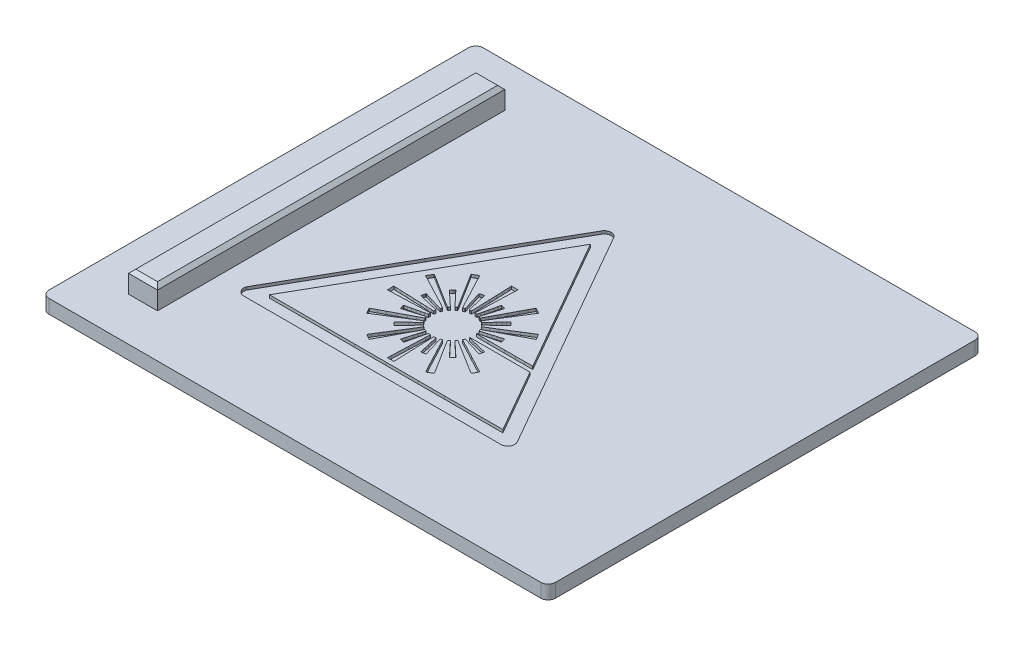
SolidWorks part; units mm, degrees
ref_plane "Front Plane" through (0, 0, 0) normal (0, 0, 1) x (1, 0, 0)
ref_plane "Top Plane" through (0, 0, 0) normal (0, 1, 0) x (1, 0, 0)
ref_plane "Right Plane" through (0, 0, 0) normal (1, 0, 0) x (0, 0, -1)
sketch "Sketch1" plane through (0, 0, 0) normal (0, 1, 0) x (1, 0, 0)
  line L1 (17.5, -15) -> (-17.5, -15)
  line L2 (17.5, -15) -> (17.5, 15)
  line L3 (17.5, 15) -> (-17.5, 15)
  line L4 (-17.5, -15) -> (-17.5, 15)
  line L5 (17.5, -15) -> (-17.5, 15) construction
  line L6 (17.5, 15) -> (-17.5, -15) construction
  point P0 (0, 0)
  dimension "D1" = 30
  dimension "D2" = 35
extrude "Boss-Extrude1" add sketch "Sketch1" along normal blind 0.95
fillet "Fillet1" radius 0.5 4 edges at (-17.5, 0.475, -15) (17.5, 0.475, -15) (17.5, 0.475, 15) (-17.5, 0.475, 15)
sketch "Sketch2" plane through (0, 0.95, 0) normal (0, 1, 0) x (1, 0, 0)
  line L7 (0, 0) -> (-13.5, 0) construction
  line L8 (-17.5, 14.5) -> (-17.5, -14.5) construction
  line L9 (-12.5, -12) -> (-14.5, -12)
  line L10 (-12.5, -12) -> (-12.5, 12)
  line L11 (-12.5, 12) -> (-14.5, 12)
  line L12 (-14.5, -12) -> (-14.5, 12)
  line L13 (-12.5, -12) -> (-14.5, 12) construction
  line L14 (-12.5, 12) -> (-14.5, -12) construction
  dimension "D1" = 24
  dimension "D2" = 2
  dimension "D3" = 3
extrude "Boss-Extrude2" add sketch "Sketch2" along normal blind 1.5
chamfer "Chamfer1" distance 0.25 angle 45 4 edges at (-13.5, 2.45, -12) (-12.5, 2.45, 0) (-13.5, 2.45, 12) (-14.5, 2.45, 0)
sketch "Sketch4" plane through (0, 0.95, 0) normal (0, 1, 0) x (1, 0, 0)
  line L0 (-9.5434, -5.1612) -> (-10.8497, -7.4519)
  line L1 (-10.4181, -8.1284) -> (-1.5285, -8.1285)
  line L2 (-1.5285, -8.1285) -> (7.3611, -8.1283)
  line L3 (7.7484, -7.3631) -> (3.3227, 0.3783)
  line L4 (3.3227, 0.3783) -> (-1.1105, 8.1325)
  line L5 (2.9967, -0.9727) -> (3.7735, -2.3341)
  line L6 (3.7721, -2.342) -> (3.2037, -2.344)
  line L7 (-0.1035, -2.307) -> (0.095, -2.2604)
  line L8 (1.0612, -2.0343) -> (1.2597, -1.987)
  line L9 (1.1727, -1.6869) -> (0.9773, -1.7453)
  line L10 (0.0274, -2.0322) -> (-0.1682, -2.0909)
  line L11 (-0.2094, -2.0255) -> (-0.2364, -1.9593)
  line L12 (-0.2364, -1.9593) -> (-0.1961, -1.9387)
  line L13 (-0.0829, -1.88) -> (1.0756, -1.267)
  line L14 (1.0756, -1.267) -> (2.2841, -0.6276)
  line L15 (2.055, -0.2524) -> (1.7026, -0.4714)
  line L16 (-0.0011, -1.5347) -> (-0.3524, -1.7512)
  line L17 (-0.3638, -1.7445) -> (-0.3758, -1.7294)
  line L18 (-0.3758, -1.7294) -> (-0.3902, -1.7114)
  line L19 (-0.3902, -1.7114) -> (-0.4058, -1.6918)
  line L20 (-0.4058, -1.6918) -> (-0.4452, -1.6421)
  line L21 (-0.4452, -1.6421) -> (-0.4032, -1.6054)
  line L22 (0.1217, -1.1166) -> (0.6047, -0.6646)
  line L23 (0.6047, -0.6646) -> (0.4958, -0.5553)
  line L24 (0.3758, -0.448) -> (0.2332, -0.5983)
  line L25 (-0.4548, -1.3302) -> (-0.5973, -1.4811)
  line L26 (-0.7053, -1.383) -> (-0.4843, -1.0296)
  line L27 (0.0507, -0.1763) -> (0.8072, 1.0284)
  line L28 (0.8072, 1.0284) -> (0.7698, 1.0506)
  line L29 (0.4158, 1.236) -> (0.2209, 0.8689)
  line L30 (-0.2494, -0.0193) -> (-0.5037, -0.5006)
  line L31 (-0.5037, -0.5006) -> (-0.7181, -0.9062)
  line L32 (-0.7181, -0.9062) -> (-0.9128, -1.2745)
  line L33 (-1.0495, -1.2211) -> (-0.9911, -1.0254)
  line L34 (-0.7038, -0.0755) -> (-0.6451, 0.1197)
  line L35 (-0.9443, 0.2198) -> (-0.9918, 0.0178)
  line L36 (-1.2195, -0.9597) -> (-1.2669, -1.162)
  line L37 (-1.3411, -1.1559) -> (-1.4119, -1.1454)
  line L38 (-1.4119, -1.1454) -> (-1.3648, 0.1365)
  line L39 (-1.3648, 0.1365) -> (-1.3463, 0.6384)
  line L40 (-1.3463, 0.6384) -> (-1.3296, 1.0858)
  line L41 (-1.3296, 1.0858) -> (-1.3154, 1.4634)
  line L42 (-1.3112, 1.5682) -> (-1.3047, 1.718)
  line L43 (-1.3047, 1.718) -> (-1.5287, 1.718)
  line L44 (-1.5287, 1.718) -> (-1.7526, 1.718)
  line L45 (-1.7526, 1.718) -> (-1.7461, 1.5682)
  line L46 (-1.7419, 1.4634) -> (-1.7277, 1.0858)
  line L47 (-1.7277, 1.0858) -> (-1.711, 0.6384)
  line L48 (-1.711, 0.6384) -> (-1.6925, 0.1365)
  line L49 (-1.6925, 0.1365) -> (-1.6454, -1.1454)
  line L50 (-1.6454, -1.1454) -> (-1.7162, -1.1559)
  line L51 (-1.7904, -1.162) -> (-1.8378, -0.9597)
  line L52 (-2.0655, 0.0178) -> (-2.1129, 0.2198)
  line L53 (-2.4122, 0.1196) -> (-2.3535, -0.0755)
  line L54 (-2.0662, -1.0254) -> (-2.0078, -1.2211)
  line L55 (-2.1445, -1.2745) -> (-2.3392, -0.9062)
  line L56 (-2.3392, -0.9062) -> (-2.5536, -0.5006)
  line L57 (-2.5536, -0.5006) -> (-2.808, -0.0193)
  line L58 (-3.2782, 0.8688) -> (-3.4731, 1.236)
  line L59 (-3.8523, 1.0121) -> (-3.1728, -0.0735)
  line L60 (-2.4601, -1.4812) -> (-2.6026, -1.3302)
  line L61 (-3.2905, -0.5983) -> (-3.4331, -0.448)
  line L62 (-3.5529, -0.5553) -> (-3.6617, -0.6645)
  line L63 (-3.6617, -0.6645) -> (-3.1893, -1.1064)
  line L64 (-2.6644, -1.5952) -> (-2.612, -1.642)
  line L65 (-2.612, -1.642) -> (-2.6515, -1.6917)
  line L66 (-2.6515, -1.6917) -> (-2.6671, -1.7114)
  line L67 (-2.6671, -1.7114) -> (-2.6814, -1.7293)
  line L68 (-2.6814, -1.7293) -> (-2.6934, -1.7444)
  line L69 (-2.7045, -1.751) -> (-3.0556, -1.5344)
  line L70 (-4.7586, -0.4715) -> (-5.1107, -0.2528)
  line L71 (-5.3431, -0.626) -> (-4.1477, -1.2585)
  line L72 (-4.1477, -1.2585) -> (-3.0399, -1.8445)
  line L73 (-4.082, -1.73) -> (-4.2269, -1.6871)
  line L74 (-4.3178, -1.9871) -> (-4.1175, -2.0344)
  line L75 (-3.1457, -2.2616) -> (-2.9453, -2.3088)
  line L76 (-2.9449, -2.386) -> (-2.9548, -2.4579)
  line L77 (-2.9548, -2.4579) -> (-3.0469, -2.4523)
  line L78 (-3.1153, -2.4489) -> (-3.4805, -2.4352)
  line L79 (-4.3938, -2.4018) -> (-4.8807, -2.3843)
  line L80 (-4.8807, -2.3843) -> (-5.3046, -2.3689)
  line L81 (-5.3046, -2.3689) -> (-5.6696, -2.3557)
  line L82 (-5.7324, -2.3532) -> (-5.8162, -2.3496)
  line L83 (-5.8162, -2.3496) -> (-5.8162, -2.5713)
  line L84 (-5.8162, -2.5713) -> (-5.8162, -2.793)
  line L85 (-5.8162, -2.793) -> (-5.7882, -2.793)
  line L86 (-5.7659, -2.7926) -> (-5.3686, -2.778)
  line L87 (-5.3686, -2.778) -> (-4.9228, -2.7617)
  line L88 (-4.9228, -2.7617) -> (-4.3989, -2.7422)
  line L89 (-4.3989, -2.7422) -> (-3.8739, -2.7228)
  line L90 (-3.4251, -2.7064) -> (-3.0286, -2.692)
  line L91 (-2.9957, -2.6914) -> (-2.9539, -2.6914)
  line L92 (-2.9539, -2.6914) -> (-2.9443, -2.7625)
  line L93 (-2.9632, -2.8411) -> (-3.1571, -2.8861)
  line L94 (-3.1571, -2.8861) -> (-3.3755, -2.9367)
  line L95 (-3.3755, -2.9367) -> (-3.6318, -2.9959)
  line L96 (-4.1065, -3.1064) -> (-4.3002, -3.1521)
  line L97 (-4.2607, -3.4161) -> (-4.2485, -3.4587)
  line L98 (-4.2442, -3.4621) -> (-4.0468, -3.4033)
  line L99 (-3.0907, -3.1146) -> (-2.8934, -3.0551)
  line L100 (-2.8422, -3.1957) -> (-3.2065, -3.3883)
  line L101 (-3.2065, -3.3883) -> (-3.6109, -3.602)
  line L102 (-3.6109, -3.602) -> (-4.089, -3.8546)
  line L103 (-4.9705, -4.3213) -> (-5.3344, -4.5147)
  line L104 (-3.614, -3.9567) -> (-2.716, -3.3947)
  line L105 (-3.1397, -3.9922) -> (-3.664, -4.4828)
  line L106 (-3.664, -4.4828) -> (-3.5512, -4.5955)
  line L107 (-3.5512, -4.5955) -> (-3.4383, -4.7082)
  line L108 (-3.4383, -4.7082) -> (-3.3903, -4.6548)
  line L109 (-3.3561, -4.6176) -> (-3.2266, -4.4787)
  line L110 (-2.9005, -4.13) -> (-2.4587, -3.6585)
  line L111 (-2.4587, -3.6585) -> (-2.4331, -3.6771)
  line L112 (-2.3754, -3.7244) -> (-2.3433, -3.7531)
  line L113 (-2.3433, -3.7531) -> (-3.1034, -4.9619)
  line L114 (-3.4773, -6.3863) -> (-3.2825, -6.0217)
  line L115 (-2.8139, -5.1386) -> (-2.5602, -4.6585)
  line L116 (-2.5602, -4.6585) -> (-2.3455, -4.2525)
  line L117 (-2.3455, -4.2525) -> (-2.152, -3.8866)
  line L118 (-2.0107, -3.9264) -> (-2.0692, -4.1251)
  line L119 (-2.1098, -5.3505) -> (-2.0633, -5.1521)
  line L120 (-1.8378, -4.1869) -> (-1.7907, -3.9884)
  line L121 (-1.7153, -3.9881) -> (-1.6471, -3.997)
  line L122 (-1.6471, -3.997) -> (-1.6491, -4.0732)
  line L123 (-1.6571, -4.3229) -> (-1.6981, -5.4408)
  line L124 (-1.6981, -5.4408) -> (-1.7408, -6.5997)
  line L125 (-1.7474, -6.7427) -> (-1.7536, -6.857)
  line L126 (-1.7536, -6.857) -> (-1.5287, -6.857)
  line L127 (-1.5287, -6.857) -> (-1.3037, -6.857)
  line L128 (-1.3037, -6.857) -> (-1.3099, -6.7427)
  line L129 (-1.3165, -6.5997) -> (-1.3592, -5.4408)
  line L130 (-1.3592, -5.4408) -> (-1.4002, -4.3229)
  line L131 (-1.4082, -4.0732) -> (-1.4102, -3.997)
  line L132 (-1.4102, -3.997) -> (-1.342, -3.9881)
  line L133 (-1.2666, -3.9884) -> (-1.2195, -4.1869)
  line L134 (-0.994, -5.1521) -> (-0.9475, -5.3505)
  line L135 (-0.6854, -5.3041) -> (-0.6423, -5.2921)
  line L136 (-0.6388, -5.2874) -> (-0.6982, -5.0883)
  line L137 (-0.9875, -4.1243) -> (-1.0451, -3.9262)
  line L138 (-0.9171, -3.873) -> (-0.7208, -4.2399)
  line L139 (0.2239, -6.019) -> (0.4202, -6.3862)
  line L140 (0.7837, -6.1347) -> (0.5825, -5.8145)
  line L141 (0.5825, -5.8145) -> (0.357, -5.4555)
  line L142 (0.357, -5.4555) -> (0.0919, -5.0333)
  line L143 (0.0919, -5.0333) -> (-0.1764, -4.606)
  line L144 (-0.1764, -4.606) -> (-0.412, -4.2308)
  line L145 (-0.412, -4.2308) -> (-0.613, -3.9106)
  line L146 (-0.613, -3.9106) -> (-0.656, -3.8423)
  line L147 (-0.656, -3.8423) -> (-0.7149, -3.7485)
  line L148 (-0.7149, -3.7485) -> (-0.6566, -3.7036)
  line L149 (-0.6566, -3.7036) -> (-0.5983, -3.6588)
  line L150 (-0.5983, -3.6588) -> (-0.1567, -4.1302)
  line L151 (0.1693, -4.4787) -> (0.2988, -4.6176)
  line L152 (0.333, -4.6548) -> (0.381, -4.7082)
  line L153 (0.381, -4.7082) -> (0.494, -4.5953)
  line L154 (0.494, -4.5953) -> (0.607, -4.4825)
  line L155 (0.607, -4.4825) -> (0.0827, -3.9919)
  line L156 (-0.3426, -3.3942) -> (0.0065, -3.6118)
  line L157 (0.8491, -4.1392) -> (1.3065, -4.4262)
  line L158 (1.6946, -4.6694) -> (2.0425, -4.8873)
  line L159 (2.2741, -4.5122) -> (1.1103, -3.8955)
  line L160 (-0.1995, -3.2034) -> (-0.2368, -3.1842)
  line L161 (-0.2368, -3.1842) -> (-0.2085, -3.1181)
  line L162 (-0.151, -3.0581) -> (0.0437, -3.1167)
  line L163 (0.992, -3.4034) -> (1.1873, -3.4618)
  line L164 (1.1913, -3.4587) -> (1.2034, -3.416)
  line L165 (1.2428, -3.1518) -> (1.0507, -3.1062)
  line L166 (0.5795, -2.9959) -> (0.3248, -2.9369)
  line L167 (0.3248, -2.9369) -> (0.1068, -2.8862)
  line L168 (0.1068, -2.8862) -> (-0.0854, -2.8416)
  line L169 (1.9618, -2.793) -> (4.0376, -2.793)
  line L170 (4.0376, -2.793) -> (5.2873, -4.9799)
  line L171 (5.2873, -4.9799) -> (6.537, -7.1669)
  line L172 (6.537, -7.1669) -> (2.5041, -7.1694)
  line L173 (-5.5617, -7.1694) -> (-9.5948, -7.1669)
  line L174 (-9.5948, -7.1669) -> (-5.5643, -0.1137)
  line L175 (-2.7162, 4.8677) -> (-1.5318, 6.9377)
  line L176 (-1.5255, 6.9376) -> (-0.7469, 5.5776)
  arc A0 (-1.6369, 8.3692) -> (-1.6998, 8.3486) centre (-1.5136, 7.886) ccw
  arc A1 (-1.6998, 8.3486) -> (-1.7595, 8.3199) centre (-1.5135, 7.8856) ccw
  arc A2 (-1.7595, 8.3199) -> (-1.8144, 8.2837) centre (-1.518, 7.8935) ccw
  arc A3 (-1.8144, 8.2837) -> (-1.8629, 8.2412) centre (-1.5384, 7.9204) ccw
  arc A4 (-1.8629, 8.2412) -> (-1.9252, 8.1593) centre (-1.5779, 7.9595) ccw
  arc A5 (-1.9252, 8.1593) -> (-2.6587, 6.8837) centre (2003.3878, -1145.6798) ccw
  arc A6 (-2.6587, 6.8837) -> (-3.797, 4.8977) centre (957.1377, -544.5622) ccw
  arc A7 (-3.797, 4.8977) -> (-6.3845, 0.3712) centre (19505.5643, -11150.5144) ccw
  arc A8 (-6.3845, 0.3712) -> (-8.0978, -2.628) centre (8611.002, -4924.3902) ccw
  arc A9 (-8.0978, -2.628) -> (-9.5434, -5.1612) centre (4419.9804, -2531.1887) ccw
  arc A10 (-10.8497, -7.4519) -> (-10.8687, -7.492) centre (-10.5976, -7.5957) ccw
  arc A11 (-10.8687, -7.492) -> (-10.8844, -7.5491) centre (-10.5798, -7.6025) ccw
  arc A12 (-10.8844, -7.5491) -> (-10.8931, -7.6209) centre (-10.2161, -7.6662) ccw
  arc A13 (-10.8931, -7.6209) -> (-10.8941, -7.6933) centre (-10.2153, -7.6662) ccw
  arc A14 (-10.8941, -7.6933) -> (-10.8861, -7.7522) centre (-10.581, -7.6808) ccw
  arc A15 (-10.8861, -7.7522) -> (-10.8392, -7.8745) centre (-10.4163, -7.6423) ccw
  arc A16 (-10.8392, -7.8745) -> (-10.7608, -7.9807) centre (-10.4046, -7.6358) ccw
  arc A17 (-10.7608, -7.9807) -> (-10.6573, -8.0623) centre (-10.4054, -7.6365) ccw
  arc A18 (-10.6573, -8.0623) -> (-10.5368, -8.1129) centre (-10.4138, -7.6507) ccw
  arc A19 (-10.5368, -8.1129) -> (-10.4181, -8.1284) centre (-10.4181, -7.6668) ccw
  arc A20 (7.3611, -8.1283) -> (7.4798, -8.1128) centre (7.3611, -7.6667) ccw
  arc A21 (7.4798, -8.1128) -> (7.5416, -8.0924) centre (7.3394, -7.5853) ccw
  arc A22 (7.5416, -8.0924) -> (7.5952, -8.0661) centre (7.3973, -7.7305) ccw
  arc A23 (7.5952, -8.0661) -> (7.6454, -8.0312) centre (7.3865, -7.7123) ccw
  arc A24 (7.6454, -8.0312) -> (7.6968, -7.9848) centre (7.2209, -7.5081) ccw
  arc A25 (7.6968, -7.9848) -> (7.7643, -7.9036) centre (7.2966, -7.584) ccw
  arc A26 (7.7643, -7.9036) -> (7.8096, -7.8169) centre (7.4202, -7.6685) ccw
  arc A27 (7.8096, -7.8169) -> (7.8332, -7.7228) centre (7.4266, -7.6709) ccw
  arc A28 (7.8332, -7.7228) -> (7.8362, -7.6192) centre (7.3064, -7.6556) ccw
  arc A29 (7.8362, -7.6192) -> (7.8323, -7.5825) centre (7.3381, -7.6534) ccw
  arc A30 (7.8323, -7.5825) -> (7.8257, -7.5458) centre (7.3205, -7.6559) ccw
  arc A31 (7.8257, -7.5458) -> (7.8168, -7.5113) centre (7.3592, -7.6475) ccw
  arc A32 (7.8168, -7.5113) -> (7.8061, -7.481) centre (7.5136, -7.6015) ccw
  arc A33 (7.8061, -7.481) -> (7.7484, -7.3631) centre (6.8601, -7.8709) ccw
  arc A34 (-1.1105, 8.1325) -> (-1.1678, 8.2158) centre (-1.6361, 7.832) ccw
  arc A35 (-1.1678, 8.2158) -> (-1.2072, 8.2563) centre (-1.4239, 8.0059) ccw
  arc A36 (-1.2072, 8.2563) -> (-1.2581, 8.2953) centre (-1.5624, 7.8458) ccw
  arc A37 (-1.2581, 8.2953) -> (-1.3146, 8.329) centre (-1.5764, 7.8251) ccw
  arc A38 (-1.3146, 8.329) -> (-1.3712, 8.3535) centre (-1.5172, 7.9391) ccw
  arc A39 (-1.3712, 8.3535) -> (-1.433, 8.3696) centre (-1.4976, 7.9947) ccw
  arc A40 (-1.433, 8.3696) -> (-1.5059, 8.378) centre (-1.5449, 7.7202) ccw
  arc A41 (-1.5059, 8.378) -> (-1.578, 8.3782) centre (-1.5439, 7.7373) ccw
  arc A42 (-1.578, 8.3782) -> (-1.6369, 8.3692) centre (-1.5618, 8.0749) ccw
  arc A43 (2.1415, 0.5253) -> (1.1256, 2.3034) centre (-7662.7608, -4377.185) ccw
  arc A44 (2.9967, -0.9727) -> (2.1415, 0.5253) centre (-3858.2555, -2204.287) ccw
  arc A45 (3.7749, -2.3393) -> (3.7735, -2.3341) centre (3.7645, -2.3393) ccw
  arc A46 (3.7721, -2.342) -> (3.7749, -2.3393) centre (3.7721, -2.3393) ccw
  arc A47 (2.576, -2.3455) -> (3.2037, -2.344) centre (2.1994, 289.3373) ccw
  arc A48 (1.8303, -2.346) -> (2.576, -2.3455) centre (1.8308, 574.7754) ccw
  arc A49 (0.6912, -2.3455) -> (1.8303, -2.346) centre (1.831, 1496.5027) ccw
  arc A50 (0.2044, -2.3434) -> (0.6912, -2.3455) centre (0.7423, 64.8165) ccw
  arc A51 (-0.1055, -2.3406) -> (0.2044, -2.3434) centre (1.2953, 133.8322) ccw
  arc A52 (-0.1202, -2.3303) -> (-0.1055, -2.3406) centre (-0.1054, -2.3246) ccw
  arc A53 (-0.1216, -2.324) -> (-0.1202, -2.3303) centre (-0.1009, -2.3229) ccw
  arc A54 (-0.1208, -2.3179) -> (-0.1216, -2.324) centre (-0.1047, -2.3231) ccw
  arc A55 (-0.118, -2.3131) -> (-0.1208, -2.3179) centre (-0.1075, -2.3222) ccw
  arc A56 (-0.1137, -2.3101) -> (-0.118, -2.3131) centre (-0.11, -2.3201) ccw
  arc A57 (-0.1035, -2.307) -> (-0.1137, -2.3101) centre (-0.0837, -2.3911) ccw
  arc A58 (0.3174, -2.2083) -> (0.095, -2.2604) centre (35.753, -154.1712) ccw
  arc A59 (0.5792, -2.1474) -> (0.3174, -2.2083) centre (67.8233, -291.7028) ccw
  arc A60 (0.5792, -2.1474) -> (0.8404, -2.0865) centre (-28.2068, 121.8061) ccw
  arc A61 (0.8404, -2.0865) -> (1.0612, -2.0343) centre (-14.0928, 61.6071) ccw
  arc A62 (1.2597, -1.987) -> (1.2647, -1.9842) centre (1.2572, -1.9766) ccw
  arc A63 (1.2647, -1.9842) -> (1.2669, -1.9769) centre (1.2592, -1.9786) ccw
  arc A64 (1.2669, -1.9769) -> (1.2501, -1.9048) centre (-10.8857, -4.7599) ccw
  arc A65 (1.2501, -1.9048) -> (1.2293, -1.8204) centre (-2.5718, -2.8039) ccw
  arc A66 (1.2293, -1.8204) -> (1.2023, -1.7186) centre (-6.9068, -3.9257) ccw
  arc A67 (1.2023, -1.7186) -> (1.198, -1.7059) centre (1.0965, -1.7474) ccw
  arc A68 (1.198, -1.7059) -> (1.1925, -1.6953) centre (1.1318, -1.7329) ccw
  arc A69 (1.1925, -1.6953) -> (1.1868, -1.6878) centre (1.151, -1.721) ccw
  arc A70 (1.1868, -1.6878) -> (1.1818, -1.6856) centre (1.1818, -1.6924) ccw
  arc A71 (1.1818, -1.6856) -> (1.1727, -1.6869) centre (1.1818, -1.7173) ccw
  arc A72 (0.9773, -1.7453) -> (0.7589, -1.8109) centre (23.3046, -76.4545) ccw
  arc A73 (0.7589, -1.8109) -> (0.5018, -1.8888) centre (44.0077, -144.998) ccw
  arc A74 (0.245, -1.9667) -> (0.5018, -1.8888) centre (-58.8196, 193.2458) ccw
  arc A75 (0.0274, -2.0322) -> (0.245, -1.9667) centre (-30.1625, 98.532) ccw
  arc A76 (-0.1745, -2.0918) -> (-0.1682, -2.0909) centre (-0.1741, -2.0713) ccw
  arc A77 (-0.1786, -2.0894) -> (-0.1745, -2.0918) centre (-0.1744, -2.0869) ccw
  arc A78 (-0.188, -2.0723) -> (-0.1786, -2.0894) centre (0.2905, -1.8206) ccw
  arc A79 (-0.1985, -2.0508) -> (-0.188, -2.0723) centre (0.1679, -1.8851) ccw
  arc A80 (-0.2094, -2.0255) -> (-0.1985, -2.0508) centre (0.4605, -1.7527) ccw
  arc A81 (-0.1961, -1.9387) -> (-0.0829, -1.88) centre (-4.0968, 5.7073) ccw
  arc A82 (2.2841, -0.6276) -> (2.2902, -0.6232) centre (2.2709, -0.6026) ccw
  arc A83 (2.2902, -0.6232) -> (2.2921, -0.6102) centre (2.283, -0.6155) ccw
  arc A84 (2.2921, -0.6102) -> (2.1859, -0.4327) centre (-51.793, -32.8523) ccw
  arc A85 (2.1859, -0.4327) -> (2.0794, -0.2562) centre (-47.1809, -30.0822) ccw
  arc A86 (2.0794, -0.2562) -> (2.0655, -0.249) centre (2.0666, -0.2639) ccw
  arc A87 (2.0655, -0.249) -> (2.055, -0.2524) centre (2.0673, -0.2722) ccw
  arc A88 (1.7026, -0.4714) -> (1.3116, -0.7151) centre (88.4426, -140.0595) ccw
  arc A89 (1.3116, -0.7151) -> (0.8498, -1.0044) centre (170.8631, -271.8705) ccw
  arc A90 (0.3884, -1.2931) -> (0.8498, -1.0044) centre (-97.4207, 155.5606) ccw
  arc A91 (-0.0011, -1.5347) -> (0.3884, -1.2931) centre (-49.1087, 78.0842) ccw
  arc A92 (-0.3592, -1.7501) -> (-0.3524, -1.7512) centre (-0.3551, -1.7468) ccw
  arc A93 (-0.3638, -1.7445) -> (-0.3592, -1.7501) centre (0.0296, -1.4296) ccw
  arc A94 (-0.4032, -1.6054) -> (-0.373, -1.5781) centre (-1.2663, -0.6173) ccw
  arc A95 (-0.373, -1.5781) -> (-0.2317, -1.4467) centre (-183.8711, 195.7959) ccw
  arc A96 (-0.2317, -1.4467) -> (-0.0664, -1.2925) centre (-96.7439, 102.2148) ccw
  arc A97 (-0.0664, -1.2925) -> (0.1217, -1.1166) centre (-162.832, 172.9716) ccw
  arc A98 (0.4958, -0.5553) -> (0.4536, -0.5134) centre (-3.2412, -4.2807) ccw
  arc A99 (0.4536, -0.5134) -> (0.4169, -0.4781) centre (-1.5288, -2.5346) ccw
  arc A100 (0.4169, -0.4781) -> (0.3847, -0.4478) centre (-6.2622, -7.5376) ccw
  arc A101 (0.3847, -0.4478) -> (0.3803, -0.446) centre (0.3803, -0.4525) ccw
  arc A102 (0.3803, -0.446) -> (0.3758, -0.448) centre (0.3803, -0.4523) ccw
  arc A103 (0.2332, -0.5983) -> (0.0752, -0.7655) centre (40.1718, -38.4763) ccw
  arc A104 (0.0752, -0.7655) -> (-0.1111, -0.9642) centre (78.5725, -74.5919) ccw
  arc A105 (-0.2974, -1.1629) -> (-0.1111, -0.9642) centre (-118.7489, 110.05) ccw
  arc A106 (-0.4548, -1.3302) -> (-0.2974, -1.1629) centre (-60.6317, 55.4845) ccw
  arc A107 (-0.6003, -1.4824) -> (-0.5973, -1.4811) centre (-0.6003, -1.4782) ccw
  arc A108 (-0.6131, -1.4778) -> (-0.6003, -1.4824) centre (-0.6003, -1.4624) ccw
  arc A109 (-0.6593, -1.4388) -> (-0.6131, -1.4778) centre (1.4298, 0.9909) ccw
  arc A110 (-0.7057, -1.3983) -> (-0.6593, -1.4388) centre (2.2094, 1.8976) ccw
  arc A111 (-0.7083, -1.3896) -> (-0.7057, -1.3983) centre (-0.7001, -1.3919) ccw
  arc A112 (-0.7053, -1.383) -> (-0.7083, -1.3896) centre (-0.6829, -1.397) ccw
  arc A113 (-0.2395, -0.6388) -> (-0.4843, -1.0296) centre (366.9365, -230.8756) ccw
  arc A114 (0.0507, -0.1763) -> (-0.2395, -0.6388) centre (718.1204, -451.0857) ccw
  arc A115 (0.7698, 1.0506) -> (0.6359, 1.1291) centre (-5.7165, -9.8696) ccw
  arc A116 (0.6359, 1.1291) -> (0.5248, 1.1916) centre (-2.2769, -3.9142) ccw
  arc A117 (0.5248, 1.1916) -> (0.4293, 1.2437) centre (-9.5731, -17.2105) ccw
  arc A118 (0.4293, 1.2437) -> (0.4204, 1.2423) centre (0.4257, 1.2371) ccw
  arc A119 (0.4204, 1.2423) -> (0.4158, 1.236) centre (0.4401, 1.2232) ccw
  arc A120 (0.2209, 0.8689) -> (0.0053, 0.4623) centre (341.2184, -180.1579) ccw
  arc A121 (0.0053, 0.4623) -> (-0.2494, -0.0193) centre (668.7742, -353.548) ccw
  arc A122 (-0.914, -1.2766) -> (-0.9128, -1.2745) centre (-0.9399, -1.2601) ccw
  arc A123 (-0.9171, -1.2776) -> (-0.914, -1.2766) centre (-0.9162, -1.2752) ccw
  arc A124 (-0.9799, -1.2531) -> (-0.9171, -1.2776) centre (11.8484, 31.4432) ccw
  arc A125 (-1.0401, -1.2293) -> (-0.9799, -1.2531) centre (3.8181, 10.976) ccw
  arc A126 (-1.0488, -1.2237) -> (-1.0401, -1.2293) centre (-1.0299, -1.2035) ccw
  arc A127 (-1.0495, -1.2211) -> (-1.0488, -1.2237) centre (-1.0471, -1.2219) ccw
  arc A128 (-0.926, -0.809) -> (-0.9911, -1.0254) centre (69.8666, -22.2011) ccw
  arc A129 (-0.8482, -0.5524) -> (-0.926, -0.809) centre (138.5664, -42.9606) ccw
  arc A130 (-0.8482, -0.5524) -> (-0.7701, -0.2949) centre (-224.3348, 67.4293) ccw
  arc A131 (-0.7701, -0.2949) -> (-0.7038, -0.0755) centre (-118.9631, 35.509) ccw
  arc A132 (-0.6451, 0.1197) -> (-0.6422, 0.1322) centre (-0.7388, 0.1479) ccw
  arc A133 (-0.6422, 0.1322) -> (-0.647, 0.1419) centre (-0.6515, 0.1337) ccw
  arc A134 (-0.647, 0.1419) -> (-0.6713, 0.1531) centre (-0.7419, -0.0331) ccw
  arc A135 (-0.6713, 0.1531) -> (-0.7136, 0.1671) centre (-0.8581, -0.3394) ccw
  arc A136 (-0.7136, 0.1671) -> (-0.7895, 0.188) centre (-1.9652, -4.2182) ccw
  arc A137 (-0.7895, 0.188) -> (-0.8471, 0.203) centre (-2.0715, -4.6167) ccw
  arc A138 (-0.8471, 0.203) -> (-0.8962, 0.215) centre (-1.4821, -2.2965) ccw
  arc A139 (-0.8962, 0.215) -> (-0.9392, 0.2249) centre (-3.3119, -10.14) ccw
  arc A140 (-0.9392, 0.2249) -> (-0.9425, 0.2237) centre (-0.9399, 0.2218) ccw
  arc A141 (-0.9425, 0.2237) -> (-0.9443, 0.2198) centre (-0.9341, 0.2175) ccw
  arc A142 (-0.9918, 0.0178) -> (-1.0442, -0.2061) centre (117.8398, -27.9011) ccw
  arc A143 (-1.0442, -0.2061) -> (-1.1058, -0.4713) centre (231.5081, -54.381) ccw
  arc A144 (-1.1673, -0.7363) -> (-1.1058, -0.4713) centre (-305.0395, 69.967) ccw
  arc A145 (-1.2195, -0.9597) -> (-1.1673, -0.7363) centre (-155.9438, 35.2761) ccw
  arc A146 (-1.2681, -1.1642) -> (-1.2669, -1.162) centre (-1.2712, -1.161) ccw
  arc A147 (-1.2701, -1.1649) -> (-1.2681, -1.1642) centre (-1.2698, -1.1624) ccw
  arc A148 (-1.2904, -1.1627) -> (-1.2701, -1.1649) centre (-0.8671, 2.5572) ccw
  arc A149 (-1.3138, -1.1598) -> (-1.2904, -1.1627) centre (-1.1633, -0.0461) ccw
  arc A150 (-1.3411, -1.1559) -> (-1.3138, -1.1598) centre (-1.0311, 0.9326) ccw
  arc A151 (-1.3112, 1.5682) -> (-1.3154, 1.4634) centre (16.9481, 0.7749) ccw
  arc A152 (-1.7419, 1.4634) -> (-1.7461, 1.5682) centre (-20.0054, 0.7749) ccw
  arc A153 (-1.7435, -1.1598) -> (-1.7162, -1.1559) centre (-2.0262, 0.9326) ccw
  arc A154 (-1.7669, -1.1627) -> (-1.7435, -1.1598) centre (-1.894, -0.0461) ccw
  arc A155 (-1.7872, -1.1649) -> (-1.7669, -1.1627) centre (-2.1903, 2.5572) ccw
  arc A156 (-1.7893, -1.1642) -> (-1.7872, -1.1649) centre (-1.7875, -1.1624) ccw
  arc A157 (-1.7904, -1.162) -> (-1.7893, -1.1642) centre (-1.7861, -1.161) ccw
  arc A158 (-1.89, -0.7363) -> (-1.8378, -0.9597) centre (152.8865, 35.2761) ccw
  arc A159 (-1.9515, -0.4713) -> (-1.89, -0.7363) centre (301.9822, 69.967) ccw
  arc A160 (-1.9515, -0.4713) -> (-2.0131, -0.2061) centre (-246.5718, -57.1635) ccw
  arc A161 (-2.0131, -0.2061) -> (-2.0655, 0.0178) centre (-126.9811, -29.3109) ccw
  arc A162 (-2.1129, 0.2198) -> (-2.1147, 0.2236) centre (-2.1228, 0.2175) ccw
  arc A163 (-2.1147, 0.2236) -> (-2.1178, 0.2247) centre (-2.1172, 0.2217) ccw
  arc A164 (-2.1178, 0.2247) -> (-2.1609, 0.2147) centre (0.4527, -10.9424) ccw
  arc A165 (-2.1609, 0.2147) -> (-2.21, 0.2028) centre (-1.5509, -2.3893) ccw
  arc A166 (-2.21, 0.2028) -> (-2.2677, 0.1877) centre (-0.9372, -4.8026) ccw
  arc A167 (-2.2677, 0.1877) -> (-2.3432, 0.1669) centre (-1.109, -4.1584) ccw
  arc A168 (-2.3432, 0.1669) -> (-2.3857, 0.1528) centre (-2.1961, -0.3488) ccw
  arc A169 (-2.3857, 0.1528) -> (-2.4103, 0.1416) centre (-2.3117, -0.0429) ccw
  arc A170 (-2.4103, 0.1416) -> (-2.4151, 0.132) centre (-2.406, 0.1335) ccw
  arc A171 (-2.4151, 0.132) -> (-2.4122, 0.1196) centre (-2.3183, 0.1479) ccw
  arc A172 (-2.3535, -0.0755) -> (-2.2873, -0.2949) centre (118.226, 36.215) ccw
  arc A173 (-2.2873, -0.2949) -> (-2.2091, -0.5524) centre (226.0242, 68.873) ccw
  arc A174 (-2.1313, -0.809) -> (-2.2091, -0.5524) centre (-141.6237, -42.9606) ccw
  arc A175 (-2.0662, -1.0254) -> (-2.1313, -0.809) centre (-72.9239, -22.2011) ccw
  arc A176 (-2.0085, -1.2237) -> (-2.0078, -1.2211) centre (-2.0102, -1.2219) ccw
  arc A177 (-2.0172, -1.2293) -> (-2.0085, -1.2237) centre (-2.0274, -1.2035) ccw
  arc A178 (-2.0774, -1.2531) -> (-2.0172, -1.2293) centre (-6.8587, 10.9352) ccw
  arc A179 (-2.1402, -1.2776) -> (-2.0774, -1.2531) centre (-14.8496, 31.305) ccw
  arc A180 (-2.1433, -1.2766) -> (-2.1402, -1.2776) centre (-2.1411, -1.2752) ccw
  arc A181 (-2.1445, -1.2745) -> (-2.1433, -1.2766) centre (-2.119, -1.261) ccw
  arc A182 (-2.808, -0.0193) -> (-3.0627, 0.4623) centre (-653.739, -343.9795) ccw
  arc A183 (-3.0627, 0.4623) -> (-3.2782, 0.8688) centre (-336.419, -176.0031) ccw
  arc A184 (-3.4731, 1.236) -> (-3.4777, 1.2422) centre (-3.4962, 1.2237) ccw
  arc A185 (-3.4777, 1.2422) -> (-3.4922, 1.2441) centre (-3.4862, 1.2337) ccw
  arc A186 (-3.4922, 1.2441) -> (-3.6713, 1.1404) centre (23.5435, -45.6589) ccw
  arc A187 (-3.6713, 1.1404) -> (-3.8499, 1.036) centre (22.9106, -44.5705) ccw
  arc A188 (-3.8499, 1.036) -> (-3.8562, 1.0221) centre (-3.8433, 1.0246) ccw
  arc A189 (-3.8562, 1.0221) -> (-3.8523, 1.0121) centre (-3.8272, 1.0278) ccw
  arc A190 (-3.1728, -0.0735) -> (-2.5706, -1.0349) centre (1904.8191, 1194.2151) ccw
  arc A191 (-2.5706, -1.0349) -> (-2.3553, -1.3759) centre (44.6014, 28.5251) ccw
  arc A192 (-2.3505, -1.3888) -> (-2.3553, -1.3759) centre (-2.3825, -1.3932) ccw
  arc A193 (-2.3531, -1.3999) -> (-2.3505, -1.3888) centre (-2.3664, -1.391) ccw
  arc A194 (-2.3652, -1.4133) -> (-2.3531, -1.3999) centre (-2.4048, -1.3653) ccw
  arc A195 (-2.3978, -1.4394) -> (-2.3652, -1.4133) centre (-3.2075, -0.3929) ccw
  arc A196 (-2.4194, -1.4558) -> (-2.3978, -1.4394) centre (-3.681, 0.2191) ccw
  arc A197 (-2.4382, -1.4697) -> (-2.4194, -1.4558) centre (-3.1162, -0.5307) ccw
  arc A198 (-2.4546, -1.4815) -> (-2.4382, -1.4697) centre (-4.2253, 1.0052) ccw
  arc A199 (-2.4573, -1.4824) -> (-2.4546, -1.4815) centre (-2.4573, -1.4776) ccw
  arc A200 (-2.4601, -1.4812) -> (-2.4573, -1.4824) centre (-2.4573, -1.4786) ccw
  arc A201 (-2.76, -1.1629) -> (-2.6026, -1.3302) centre (63.0691, 60.6258) ccw
  arc A202 (-2.9462, -0.9642) -> (-2.76, -1.1629) centre (126.4969, 120.1608) ccw
  arc A203 (-2.9462, -0.9642) -> (-3.1326, -0.7655) centre (-81.6298, -74.5919) ccw
  arc A204 (-3.1326, -0.7655) -> (-3.2905, -0.5983) centre (-43.2291, -38.4763) ccw
  arc A205 (-3.4331, -0.448) -> (-3.4376, -0.446) centre (-3.4376, -0.4523) ccw
  arc A206 (-3.4376, -0.446) -> (-3.442, -0.4478) centre (-3.4376, -0.4525) ccw
  arc A207 (-3.442, -0.4478) -> (-3.4742, -0.4781) centre (3.1903, -7.5149) ccw
  arc A208 (-3.4742, -0.4781) -> (-3.5108, -0.5134) centre (-1.5323, -2.5285) ccw
  arc A209 (-3.5108, -0.5134) -> (-3.5529, -0.5553) centre (0.1773, -4.2697) ccw
  arc A210 (-3.1893, -1.1064) -> (-3.0045, -1.2792) centre (178.3371, 192.9231) ccw
  arc A211 (-3.0045, -1.2792) -> (-2.8402, -1.4323) centre (110.0228, 119.764) ccw
  arc A212 (-2.8402, -1.4323) -> (-2.7011, -1.5618) centre (173.0885, 187.4868) ccw
  arc A213 (-2.7011, -1.5618) -> (-2.6644, -1.5952) centre (-1.0529, 0.2108) ccw
  arc A214 (-2.6979, -1.7499) -> (-2.6934, -1.7444) centre (-3.1401, -1.3874) ccw
  arc A215 (-2.7045, -1.751) -> (-2.6979, -1.7499) centre (-2.7018, -1.7467) ccw
  arc A216 (-3.4449, -1.2929) -> (-3.0556, -1.5344) centre (47.3172, 80.0901) ccw
  arc A217 (-3.9059, -1.0044) -> (-3.4449, -1.2929) centre (96.9187, 159.6123) ccw
  arc A218 (-3.9059, -1.0044) -> (-4.3675, -0.7152) centre (-164.7912, -257.2997) ccw
  arc A219 (-4.3675, -0.7152) -> (-4.7586, -0.4715) centre (-86.889, -132.7017) ccw
  arc A220 (-5.1107, -0.2528) -> (-5.1218, -0.2492) centre (-5.1239, -0.2742) ccw
  arc A221 (-5.1218, -0.2492) -> (-5.1366, -0.2567) centre (-5.1232, -0.2649) ccw
  arc A222 (-5.1366, -0.2567) -> (-5.2433, -0.4326) centre (38.4351, -26.8004) ccw
  arc A223 (-5.2433, -0.4326) -> (-5.3496, -0.6095) centre (42.7186, -29.3863) ccw
  arc A224 (-5.3496, -0.6095) -> (-5.3475, -0.623) centre (-5.3404, -0.615) ccw
  arc A225 (-5.3475, -0.623) -> (-5.3431, -0.626) centre (-5.3324, -0.6058) ccw
  arc A226 (-3.0399, -1.8445) -> (-2.8375, -1.9509) centre (18.8497, 39.5397) ccw
  arc A227 (-2.8295, -1.9585) -> (-2.8375, -1.9509) centre (-2.847, -1.9691) ccw
  arc A228 (-2.8274, -1.9684) -> (-2.8295, -1.9585) centre (-2.8426, -1.9664) ccw
  arc A229 (-2.8317, -1.9853) -> (-2.8274, -1.9684) centre (-2.8993, -1.9588) ccw
  arc A230 (-2.8472, -2.0233) -> (-2.8317, -1.9853) centre (-4.3694, -1.3836) ccw
  arc A231 (-2.8576, -2.048) -> (-2.8472, -2.0233) centre (-7.8817, 0.0925) ccw
  arc A232 (-2.8668, -2.0693) -> (-2.8576, -2.048) centre (-5.7374, -0.821) ccw
  arc A233 (-2.8748, -2.0877) -> (-2.8668, -2.0693) centre (-9.5871, 0.853) ccw
  arc A234 (-2.8764, -2.0906) -> (-2.8748, -2.0877) centre (-2.8916, -2.0803) ccw
  arc A235 (-2.8819, -2.0926) -> (-2.8764, -2.0906) centre (-2.8805, -2.0879) ccw
  arc A236 (-3.0153, -2.0529) -> (-2.8819, -2.0926) centre (28.7721, 104.5154) ccw
  arc A237 (-3.2246, -1.9898) -> (-3.0153, -2.0529) centre (8.8022, 37.5658) ccw
  arc A238 (-3.7272, -1.8369) -> (-3.2246, -1.9898) centre (288.3979, 957.1437) ccw
  arc A239 (-3.7272, -1.8369) -> (-3.9186, -1.7789) centre (-24.1057, -68.7348) ccw
  arc A240 (-3.9186, -1.7789) -> (-4.082, -1.73) centre (-14.6402, -37.3397) ccw
  arc A241 (-4.2269, -1.6871) -> (-4.2375, -1.6856) centre (-4.2375, -1.7229) ccw
  arc A242 (-4.2375, -1.6856) -> (-4.2432, -1.6876) centre (-4.2375, -1.6947) ccw
  arc A243 (-4.2432, -1.6876) -> (-4.2492, -1.6938) centre (-4.2226, -1.7132) ccw
  arc A244 (-4.2492, -1.6938) -> (-4.2544, -1.7028) centre (-4.2106, -1.722) ccw
  arc A245 (-4.2544, -1.7028) -> (-4.258, -1.7135) centre (-4.1946, -1.729) ccw
  arc A246 (-4.2623, -1.7306) -> (-4.258, -1.7135) centre (-5.1596, -1.4931) ccw
  arc A247 (-4.2724, -1.7684) -> (-4.2623, -1.7306) centre (-20.8568, 2.6617) ccw
  arc A248 (-4.2844, -1.8132) -> (-4.2724, -1.7684) centre (-20.8161, 2.6508) ccw
  arc A249 (-4.2974, -1.8611) -> (-4.2844, -1.8132) centre (-25.7723, 3.9892) ccw
  arc A250 (-4.2974, -1.8611) -> (-4.3094, -1.9073) centre (-2.2238, -2.426) ccw
  arc A251 (-4.3094, -1.9073) -> (-4.3185, -1.9468) centre (-3.2152, -2.1794) ccw
  arc A252 (-4.3185, -1.9468) -> (-4.3254, -1.9804) centre (-1.8004, -2.4777) ccw
  arc A253 (-4.3254, -1.9804) -> (-4.3235, -1.9848) centre (-4.3213, -1.9812) ccw
  arc A254 (-4.3235, -1.9848) -> (-4.3178, -1.9871) centre (-4.3134, -1.9685) ccw
  arc A255 (-4.1175, -2.0344) -> (-3.8948, -2.0867) centre (20.4419, 102.0274) ccw
  arc A256 (-3.8948, -2.0867) -> (-3.6315, -2.1481) centre (43.2956, 199.7967) ccw
  arc A257 (-3.3682, -2.2094) -> (-3.6315, -2.1481) centre (-60.6978, -247.7268) ccw
  arc A258 (-3.1457, -2.2616) -> (-3.3682, -2.2094) centre (-32.8298, -128.3812) ccw
  arc A259 (-2.9405, -2.3107) -> (-2.9453, -2.3088) centre (-2.9491, -2.3249) ccw
  arc A260 (-2.9386, -2.3143) -> (-2.9405, -2.3107) centre (-2.9425, -2.3141) ccw
  arc A261 (-2.9395, -2.3342) -> (-2.9386, -2.3143) centre (-3.7591, -2.286) ccw
  arc A262 (-2.9415, -2.3582) -> (-2.9395, -2.3342) centre (-3.4387, -2.3049) ccw
  arc A263 (-2.9449, -2.386) -> (-2.9415, -2.3582) centre (-3.8541, -2.2603) ccw
  arc A264 (-3.0469, -2.4523) -> (-3.1153, -2.4489) centre (-3.2311, -5.5027) ccw
  arc A265 (-3.4805, -2.4352) -> (-3.9063, -2.4194) centre (-19.3951, -426.4459) ccw
  arc A266 (-3.9063, -2.4194) -> (-4.3938, -2.4018) centre (-30.406, -727.8751) ccw
  arc A267 (-5.7324, -2.3532) -> (-5.6696, -2.3557) centre (-5.3072, 7.605) ccw
  arc A268 (-5.7882, -2.793) -> (-5.7659, -2.7926) centre (-5.789, -2.1588) ccw
  arc A269 (-3.4251, -2.7064) -> (-3.8739, -2.7228) centre (21.0338, -678.7257) ccw
  arc A270 (-2.9957, -2.6914) -> (-3.0286, -2.692) centre (-2.9949, -3.6262) ccw
  arc A271 (-2.9394, -2.8022) -> (-2.9443, -2.7625) centre (-4.4286, -2.9634) ccw
  arc A272 (-2.9392, -2.8217) -> (-2.9394, -2.8022) centre (-3.0414, -2.8133) ccw
  arc A273 (-2.9428, -2.8322) -> (-2.9392, -2.8217) centre (-2.9622, -2.8198) ccw
  arc A274 (-2.9505, -2.8379) -> (-2.9428, -2.8322) centre (-2.9541, -2.825) ccw
  arc A275 (-2.9632, -2.8411) -> (-2.9505, -2.8379) centre (-3.0326, -2.5419) ccw
  arc A276 (-3.6318, -2.9959) -> (-3.8881, -3.0552) centre (28.3077, -141.4102) ccw
  arc A277 (-3.8881, -3.0552) -> (-4.1065, -3.1064) centre (13.2243, -76.5919) ccw
  arc A278 (-4.3002, -3.1521) -> (-4.3135, -3.1566) centre (-4.2828, -3.2257) ccw
  arc A279 (-4.3135, -3.1566) -> (-4.3207, -3.1665) centre (-4.3085, -3.1678) ccw
  arc A280 (-4.3207, -3.1665) -> (-4.3202, -3.1875) centre (-4.24, -3.1752) ccw
  arc A281 (-4.3202, -3.1875) -> (-4.3123, -3.2261) centre (-3.9333, -3.128) ccw
  arc A282 (-4.3123, -3.2261) -> (-4.2897, -3.3112) centre (2.9108, -1.3567) ccw
  arc A283 (-4.2897, -3.3112) -> (-4.2742, -3.3679) centre (7.4394, -0.1274) ccw
  arc A284 (-4.2742, -3.3679) -> (-4.2607, -3.4161) centre (1.9189, -1.6546) ccw
  arc A285 (-4.2485, -3.4587) -> (-4.2469, -3.4614) centre (-4.2424, -3.4569) ccw
  arc A286 (-4.2469, -3.4614) -> (-4.2442, -3.4621) centre (-4.245, -3.4594) ccw
  arc A287 (-4.0468, -3.4033) -> (-3.8285, -3.3378) centre (-24.6983, 65.9024) ccw
  arc A288 (-3.8285, -3.3378) -> (-3.5696, -3.2595) centre (-44.9855, 133.209) ccw
  arc A289 (-3.3104, -3.181) -> (-3.5696, -3.2595) centre (117.0784, -400.8031) ccw
  arc A290 (-3.0907, -3.1146) -> (-3.3104, -3.181) centre (58.962, -208.8544) ccw
  arc A291 (-2.8864, -3.0535) -> (-2.8934, -3.0551) centre (-2.8782, -3.1056) ccw
  arc A292 (-2.8729, -3.0608) -> (-2.8864, -3.0535) centre (-2.8844, -3.0659) ccw
  arc A293 (-2.8486, -3.1184) -> (-2.8729, -3.0608) centre (-4.0553, -3.5928) ccw
  arc A294 (-2.8272, -3.1771) -> (-2.8486, -3.1184) centre (-4.0639, -3.5962) ccw
  arc A295 (-2.8325, -3.1906) -> (-2.8272, -3.1771) centre (-2.8378, -3.1807) ccw
  arc A296 (-2.8422, -3.1957) -> (-2.8325, -3.1906) centre (-3.5224, -1.9085) ccw
  arc A297 (-4.089, -3.8546) -> (-4.5668, -4.1073) centre (309.9915, -598.2768) ccw
  arc A298 (-4.5668, -4.1073) -> (-4.9705, -4.3213) centre (156.8968, -309.0968) ccw
  arc A299 (-5.3344, -4.5147) -> (-5.342, -4.5201) centre (-5.3177, -4.5462) ccw
  arc A300 (-5.342, -4.5201) -> (-5.3435, -4.5296) centre (-5.3367, -4.5258) ccw
  arc A301 (-5.3435, -4.5296) -> (-5.2468, -4.7058) centre (93.7286, 49.7545) ccw
  arc A302 (-5.2468, -4.7058) -> (-5.1551, -4.8712) centre (21.1577, 9.823) ccw
  arc A303 (-5.1551, -4.8712) -> (-5.1307, -4.9042) centre (-5.015, -4.793) ccw
  arc A304 (-5.1307, -4.9042) -> (-5.1281, -4.9046) centre (-5.1292, -4.9028) ccw
  arc A305 (-5.1281, -4.9046) -> (-5.0992, -4.8877) centre (-8.7875, 1.4221) ccw
  arc A306 (-5.0992, -4.8877) -> (-5.0661, -4.8679) centre (-6.017, -3.3175) ccw
  arc A307 (-5.0661, -4.8679) -> (-5.0275, -4.8439) centre (-6.9215, -1.8427) ccw
  arc A308 (-4.424, -4.4641) -> (-5.0275, -4.8439) centre (137.3949, -230.5228) ccw
  arc A309 (-3.614, -3.9567) -> (-4.424, -4.4641) centre (442.6895, -717.1612) ccw
  arc A310 (-2.708, -3.3924) -> (-2.716, -3.3947) centre (-2.708, -3.4075) ccw
  arc A311 (-2.7013, -3.3954) -> (-2.708, -3.3924) centre (-2.708, -3.4016) ccw
  arc A312 (-2.6811, -3.4183) -> (-2.7013, -3.3954) centre (-3.5349, -4.1517) ccw
  arc A313 (-2.6559, -3.449) -> (-2.6811, -3.4183) centre (-3.3841, -4.0222) ccw
  arc A314 (-2.6241, -3.4902) -> (-2.6559, -3.449) centre (-4.7816, -5.1224) ccw
  arc A315 (-2.6248, -3.5004) -> (-2.6241, -3.4902) centre (-2.6302, -3.4949) ccw
  arc A316 (-2.7502, -3.6228) -> (-2.6248, -3.5004) centre (-43.6573, 38.3954) ccw
  arc A317 (-2.9101, -3.7763) -> (-2.7502, -3.6228) centre (-13.3845, 7.3004) ccw
  arc A318 (-3.1397, -3.9922) -> (-2.9101, -3.7763) centre (-44.2067, 39.8948) ccw
  arc A319 (-3.3561, -4.6176) -> (-3.3903, -4.6548) centre (-1.1293, -6.6932) ccw
  arc A320 (-3.0732, -4.3145) -> (-3.2266, -4.4787) centre (142.886, -140.8447) ccw
  arc A321 (-2.9005, -4.13) -> (-3.0732, -4.3145) centre (229.9875, -222.3189) ccw
  arc A322 (-2.421, -3.6863) -> (-2.4331, -3.6771) centre (-2.6566, -3.9847) ccw
  arc A323 (-2.4056, -3.6987) -> (-2.421, -3.6863) centre (-3.0959, -4.5411) ccw
  arc A324 (-2.3896, -3.7121) -> (-2.4056, -3.6987) centre (-3.1409, -4.596) ccw
  arc A325 (-2.3754, -3.7244) -> (-2.3896, -3.7121) centre (-2.882, -4.2915) ccw
  arc A326 (-3.1034, -4.9619) -> (-3.5375, -5.6532) centre (458.8188, -295.4443) ccw
  arc A327 (-3.5375, -5.6532) -> (-3.7301, -5.965) centre (20.8419, -20.9335) ccw
  arc A328 (-3.7301, -5.965) -> (-3.8506, -6.1642) centre (30.0912, -26.5679) ccw
  arc A329 (-3.8506, -6.1642) -> (-3.8467, -6.1821) centre (-3.8392, -6.171) ccw
  arc A330 (-3.8467, -6.1821) -> (-3.7985, -6.2122) centre (-3.4255, -5.5622) ccw
  arc A331 (-3.7985, -6.2122) -> (-3.6524, -6.2956) centre (13.9668, 24.7408) ccw
  arc A332 (-3.6524, -6.2956) -> (-3.4913, -6.387) centre (109.5277, 193.0714) ccw
  arc A333 (-3.4913, -6.387) -> (-3.4818, -6.3892) centre (-3.4828, -6.3721) ccw
  arc A334 (-3.4818, -6.3892) -> (-3.4773, -6.3863) centre (-3.4821, -6.3837) ccw
  arc A335 (-3.2825, -6.0217) -> (-3.0677, -5.618) centre (-145.3104, 69.8328) ccw
  arc A336 (-3.0677, -5.618) -> (-2.8139, -5.1386) centre (-282.9637, 142.8491) ccw
  arc A337 (-2.1468, -3.8776) -> (-2.152, -3.8866) centre (-2.0117, -3.9608) ccw
  arc A338 (-2.135, -3.8729) -> (-2.1468, -3.8776) centre (-2.1378, -3.8832) ccw
  arc A339 (-2.0804, -3.889) -> (-2.135, -3.8729) centre (-2.5208, -5.2837) ccw
  arc A340 (-2.0274, -3.9073) -> (-2.0804, -3.889) centre (-2.4072, -4.9241) ccw
  arc A341 (-2.0115, -3.9203) -> (-2.0274, -3.9073) centre (-2.0386, -3.937) ccw
  arc A342 (-2.0107, -3.9264) -> (-2.0115, -3.9203) centre (-2.018, -3.9243) ccw
  arc A343 (-2.135, -4.3461) -> (-2.0692, -4.1251) centre (-42.8005, 7.8799) ccw
  arc A344 (-2.214, -4.6073) -> (-2.135, -4.3461) centre (-81.4258, 19.4926) ccw
  arc A345 (-2.214, -4.6073) -> (-2.3393, -5.0207) centre (177.442, -59.2672) ccw
  arc A346 (-2.3393, -5.0207) -> (-2.3862, -5.1842) centre (3.8424, -6.8859) ccw
  arc A347 (-2.3862, -5.1842) -> (-2.4103, -5.2783) centre (0.5152, -5.9769) ccw
  arc A348 (-2.4103, -5.2783) -> (-2.4018, -5.2945) centre (-2.3969, -5.2815) ccw
  arc A349 (-2.4018, -5.2945) -> (-2.3887, -5.2988) centre (-2.3428, -5.1377) ccw
  arc A350 (-2.3887, -5.2988) -> (-2.3492, -5.3099) centre (-0.1208, 2.6527) ccw
  arc A351 (-2.3492, -5.3099) -> (-2.302, -5.323) centre (-0.5695, 1.0491) ccw
  arc A352 (-2.302, -5.323) -> (-2.2497, -5.337) centre (0.2929, 4.2211) ccw
  arc A353 (-2.2497, -5.337) -> (-2.1872, -5.353) centre (-1.4273, -2.2453) ccw
  arc A354 (-2.1872, -5.353) -> (-2.1467, -5.3614) centre (-2.05, -4.7918) ccw
  arc A355 (-2.1467, -5.3614) -> (-2.1196, -5.3649) centre (-2.0893, -5.023) ccw
  arc A356 (-2.1196, -5.3649) -> (-2.1126, -5.3603) centre (-2.119, -5.3581) ccw
  arc A357 (-2.1126, -5.3603) -> (-2.1098, -5.3505) centre (-2.2063, -5.3278) ccw
  arc A358 (-2.0633, -5.1521) -> (-2.0114, -4.9299) centre (-191.6081, 39.2206) ccw
  arc A359 (-2.0114, -4.9299) -> (-1.9506, -4.6684) centre (-365.1964, 79.6433) ccw
  arc A360 (-1.8898, -4.4074) -> (-1.9506, -4.6684) centre (137.804, -37.1062) ccw
  arc A361 (-1.8378, -4.1869) -> (-1.8898, -4.4074) centre (69.8227, -21.1935) ccw
  arc A362 (-1.7882, -3.9839) -> (-1.7907, -3.9884) centre (-1.7815, -3.9906) ccw
  arc A363 (-1.7842, -3.9823) -> (-1.7882, -3.9839) centre (-1.7844, -3.9877) ccw
  arc A364 (-1.7649, -3.9832) -> (-1.7842, -3.9823) centre (-1.8145, -4.8413) ccw
  arc A365 (-1.7418, -3.985) -> (-1.7649, -3.9832) centre (-1.7958, -4.5188) ccw
  arc A366 (-1.7153, -3.9881) -> (-1.7418, -3.985) centre (-1.8367, -4.9228) ccw
  arc A367 (-1.6571, -4.3229) -> (-1.6491, -4.0732) centre (-28.1191, -3.3556) ccw
  arc A368 (-1.7474, -6.7427) -> (-1.7408, -6.5997) centre (-9.76, -6.3035) ccw
  arc A369 (-1.3165, -6.5997) -> (-1.3099, -6.7427) centre (6.7027, -6.3035) ccw
  arc A370 (-1.4082, -4.0732) -> (-1.4002, -4.3229) centre (25.0618, -3.3556) ccw
  arc A371 (-1.3155, -3.985) -> (-1.342, -3.9881) centre (-1.2206, -4.9228) ccw
  arc A372 (-1.2924, -3.9832) -> (-1.3155, -3.985) centre (-1.2615, -4.5188) ccw
  arc A373 (-1.2731, -3.9823) -> (-1.2924, -3.9832) centre (-1.2428, -4.8413) ccw
  arc A374 (-1.2691, -3.9839) -> (-1.2731, -3.9823) centre (-1.2729, -3.9877) ccw
  arc A375 (-1.2666, -3.9884) -> (-1.2691, -3.9839) centre (-1.2758, -3.9906) ccw
  arc A376 (-1.1675, -4.4074) -> (-1.2195, -4.1869) centre (-72.88, -21.1935) ccw
  arc A377 (-1.1067, -4.6684) -> (-1.1675, -4.4074) centre (-140.8613, -37.1062) ccw
  arc A378 (-1.1067, -4.6684) -> (-1.0459, -4.9299) centre (364.1619, 80.1126) ccw
  arc A379 (-1.0459, -4.9299) -> (-0.994, -5.1521) centre (189.841, 39.5199) ccw
  arc A380 (-0.9475, -5.3505) -> (-0.9447, -5.3602) centre (-0.8513, -5.3279) ccw
  arc A381 (-0.9447, -5.3602) -> (-0.9376, -5.3647) centre (-0.9383, -5.358) ccw
  arc A382 (-0.9376, -5.3647) -> (-0.9065, -5.3602) centre (-0.9956, -4.8621) ccw
  arc A383 (-0.9065, -5.3602) -> (-0.861, -5.3506) centre (-1.0361, -4.6355) ccw
  arc A384 (-0.861, -5.3506) -> (-0.7915, -5.3329) centre (-1.7929, -1.5441) ccw
  arc A385 (-0.7915, -5.3329) -> (-0.7341, -5.3175) centre (-3.5862, 5.2409) ccw
  arc A386 (-0.7341, -5.3175) -> (-0.6854, -5.3041) centre (-2.2442, 0.2727) ccw
  arc A387 (-0.6423, -5.2921) -> (-0.6395, -5.2904) centre (-0.644, -5.2861) ccw
  arc A388 (-0.6395, -5.2904) -> (-0.6388, -5.2874) centre (-0.6417, -5.2883) ccw
  arc A389 (-0.6982, -5.0883) -> (-0.7644, -4.8679) centre (-68.5801, -25.3454) ccw
  arc A390 (-0.7644, -4.8679) -> (-0.8435, -4.6067) centre (-134.3269, -45.198) ccw
  arc A391 (-0.9223, -4.3454) -> (-0.8435, -4.6067) centre (55.7917, 12.6156) ccw
  arc A392 (-0.9875, -4.1243) -> (-0.9223, -4.3454) centre (28.0242, 4.3114) ccw
  arc A393 (-1.0432, -3.9201) -> (-1.0451, -3.9262) centre (-1.0394, -3.9246) ccw
  arc A394 (-1.0296, -3.9116) -> (-1.0432, -3.9201) centre (-1.0077, -3.9622) ccw
  arc A395 (-0.9828, -3.8919) -> (-1.0296, -3.9116) centre (0.2561, -6.885) ccw
  arc A396 (-0.935, -3.8724) -> (-0.9828, -3.8919) centre (0.5371, -7.564) ccw
  arc A397 (-0.9221, -3.87) -> (-0.935, -3.8724) centre (-0.9221, -3.9047) ccw
  arc A398 (-0.9171, -3.873) -> (-0.9221, -3.87) centre (-0.9221, -3.8757) ccw
  arc A399 (-0.5041, -4.6465) -> (-0.7208, -4.2399) centre (-126.2463, -71.3928) ccw
  arc A400 (-0.2484, -5.1294) -> (-0.5041, -4.6465) centre (-248.2772, -136.1687) ccw
  arc A401 (-0.2484, -5.1294) -> (0.0073, -5.6123) centre (266.4032, 135.7484) ccw
  arc A402 (0.0073, -5.6123) -> (0.2239, -6.019) centre (135.3037, 66.1815) ccw
  arc A403 (0.4202, -6.3862) -> (0.425, -6.3892) centre (0.4253, -6.3834) ccw
  arc A404 (0.425, -6.3892) -> (0.4309, -6.3879) centre (0.4256, -6.3782) ccw
  arc A405 (0.4309, -6.3879) -> (0.4858, -6.3577) centre (-10.9105, 14.3363) ccw
  arc A406 (0.4858, -6.3577) -> (0.5482, -6.3229) centre (-2.3853, -1.1442) ccw
  arc A407 (0.5482, -6.3229) -> (0.6207, -6.2814) centre (-4.9105, 3.3137) ccw
  arc A408 (0.6207, -6.2814) -> (0.7396, -6.2123) centre (-8.4559, 9.4639) ccw
  arc A409 (0.7396, -6.2123) -> (0.7802, -6.1854) centre (0.515, -5.8294) ccw
  arc A410 (0.7802, -6.1854) -> (0.7953, -6.168) centre (0.7483, -6.1425) ccw
  arc A411 (0.7953, -6.168) -> (0.7946, -6.1519) centre (0.7814, -6.1605) ccw
  arc A412 (0.7837, -6.1347) -> (0.7946, -6.1519) centre (2.0039, -5.3681) ccw
  arc A413 (0.016, -4.3146) -> (-0.1567, -4.1302) centre (-232.9796, -222.2582) ccw
  arc A414 (0.1693, -4.4787) -> (0.016, -4.3146) centre (-145.9046, -140.8086) ccw
  arc A415 (0.333, -4.6548) -> (0.2988, -4.6176) centre (-1.9279, -6.6932) ccw
  arc A416 (-0.1438, -3.7788) -> (0.0827, -3.9919) centre (39.7295, 38.3744) ccw
  arc A417 (-0.3047, -3.6245) -> (-0.1438, -3.7788) centre (10.7136, 7.6995) ccw
  arc A418 (-0.4324, -3.4999) -> (-0.3047, -3.6245) centre (45.5664, 43.5192) ccw
  arc A419 (-0.4331, -3.49) -> (-0.4324, -3.4999) centre (-0.4271, -3.4946) ccw
  arc A420 (-0.4012, -3.4487) -> (-0.4331, -3.49) centre (1.6209, -5.0414) ccw
  arc A421 (-0.376, -3.4181) -> (-0.4012, -3.4487) centre (0.2789, -3.9844) ccw
  arc A422 (-0.3559, -3.3956) -> (-0.376, -3.4181) centre (0.3614, -4.0557) ccw
  arc A423 (-0.3487, -3.3924) -> (-0.3559, -3.3956) centre (-0.3487, -3.4022) ccw
  arc A424 (-0.3426, -3.3942) -> (-0.3487, -3.3924) centre (-0.3487, -3.4041) ccw
  arc A425 (0.3924, -3.8529) -> (0.0065, -3.6118) centre (-125.882, -205.5449) ccw
  arc A426 (0.8491, -4.1392) -> (0.3924, -3.8529) centre (-247.9322, -400.4898) ccw
  arc A427 (1.3065, -4.4262) -> (1.6946, -4.6694) centre (404.1385, 637.8787) ccw
  arc A428 (2.0425, -4.8873) -> (2.0565, -4.8954) centre (2.1689, -4.6854) ccw
  arc A429 (2.0565, -4.8954) -> (2.0703, -4.8935) centre (2.0621, -4.8851) ccw
  arc A430 (2.0703, -4.8935) -> (2.0906, -4.8697) centre (1.9456, -4.7668) ccw
  arc A431 (2.0906, -4.8697) -> (2.1218, -4.8217) centre (1.5129, -4.4597) ccw
  arc A432 (2.1218, -4.8217) -> (2.1836, -4.7164) centre (-7.8173, 1.0867) ccw
  arc A433 (2.1836, -4.7164) -> (2.225, -4.6435) centre (-1.5552, -2.5469) ccw
  arc A434 (2.225, -4.6435) -> (2.2584, -4.5809) centre (0.2634, -3.5556) ccw
  arc A435 (2.2584, -4.5809) -> (2.2859, -4.5268) centre (-2.9976, -1.8797) ccw
  arc A436 (2.2859, -4.5268) -> (2.2847, -4.5198) centre (2.2805, -4.5241) ccw
  arc A437 (2.2847, -4.5198) -> (2.2741, -4.5122) centre (2.2518, -4.5543) ccw
  arc A438 (1.1103, -3.8955) -> (0.0452, -3.3312) centre (-1855.4505, -3507.2777) ccw
  arc A439 (0.0452, -3.3312) -> (-0.1995, -3.2034) centre (-11.6084, -25.338) ccw
  arc A440 (-0.1945, -3.0878) -> (-0.2085, -3.1181) centre (0.3873, -3.3737) ccw
  arc A441 (-0.183, -3.0684) -> (-0.1945, -3.0878) centre (-0.0668, -3.1506) ccw
  arc A442 (-0.1729, -3.0574) -> (-0.183, -3.0684) centre (-0.1357, -3.1018) ccw
  arc A443 (-0.1638, -3.055) -> (-0.1729, -3.0574) centre (-0.1658, -3.0659) ccw
  arc A444 (-0.151, -3.0581) -> (-0.1638, -3.055) centre (-0.1839, -3.1675) ccw
  arc A445 (0.2628, -3.1828) -> (0.0437, -3.1167) centre (-38.9517, -132.6456) ccw
  arc A446 (0.5199, -3.2608) -> (0.2628, -3.1828) centre (-73.7561, -247.5487) ccw
  arc A447 (0.5199, -3.2608) -> (0.776, -3.3385) centre (44.7496, 142.2071) ccw
  arc A448 (0.776, -3.3385) -> (0.992, -3.4034) centre (23.1169, 70.6062) ccw
  arc A449 (1.1873, -3.4618) -> (1.1899, -3.4611) centre (1.1881, -3.4594) ccw
  arc A450 (1.1899, -3.4611) -> (1.1913, -3.4587) centre (1.1857, -3.4571) ccw
  arc A451 (1.2034, -3.416) -> (1.2169, -3.3678) centre (-5.5222, -1.5065) ccw
  arc A452 (1.2169, -3.3678) -> (1.2324, -3.3112) centre (-11.5847, 0.1679) ccw
  arc A453 (1.2324, -3.3112) -> (1.255, -3.226) centre (-5.9805, -1.3533) ccw
  arc A454 (1.255, -3.226) -> (1.2629, -3.1874) centre (0.8769, -3.1282) ccw
  arc A455 (1.2629, -3.1874) -> (1.2634, -3.1664) centre (1.1829, -3.1752) ccw
  arc A456 (1.2634, -3.1664) -> (1.2562, -3.1564) centre (1.251, -3.1678) ccw
  arc A457 (1.2562, -3.1564) -> (1.2428, -3.1518) centre (1.2261, -3.2221) ccw
  arc A458 (1.0507, -3.1062) -> (0.8339, -3.0551) centre (-15.1984, -71.6126) ccw
  arc A459 (0.8339, -3.0551) -> (0.5795, -2.9959) centre (-29.3207, -132.0014) ccw
  arc A460 (-0.1025, -2.8374) -> (-0.0854, -2.8416) centre (0.1578, -1.7948) ccw
  arc A461 (-0.1122, -2.8338) -> (-0.1025, -2.8374) centre (-0.0914, -2.7926) ccw
  arc A462 (-0.118, -2.8287) -> (-0.1122, -2.8338) centre (-0.1054, -2.8204) ccw
  arc A463 (-0.1202, -2.8218) -> (-0.118, -2.8287) centre (-0.1069, -2.8214) ccw
  arc A464 (-0.1191, -2.8125) -> (-0.1202, -2.8218) centre (-0.0874, -2.8208) ccw
  arc A465 (-0.1016, -2.7987) -> (-0.1191, -2.8125) centre (-0.1013, -2.8172) ccw
  arc A466 (0.1587, -2.7956) -> (-0.1016, -2.7987) centre (0.5931, -49.1171) ccw
  arc A467 (0.6062, -2.7934) -> (0.1587, -2.7956) centre (0.6327, -53.3467) ccw
  arc A468 (1.9618, -2.793) -> (0.6062, -2.7934) centre (1.9617, -2589.699) ccw
  arc A469 (0.6683, -7.1702) -> (2.5041, -7.1694) centre (-0.4035, 4582.5049) ccw
  arc A470 (-1.5287, -7.1705) -> (0.6683, -7.1702) centre (-1.5196, 9302.2027) ccw
  arc A471 (-3.7258, -7.1702) -> (-1.5287, -7.1705) centre (-1.5378, 9302.3123) ccw
  arc A472 (-5.5617, -7.1694) -> (-3.7258, -7.1702) centre (-2.6541, 4582.7209) ccw
  arc A473 (-4.0184, 2.5909) -> (-5.5643, -0.1137) centre (13252.8133, -7576.5678) ccw
  arc A474 (-2.7162, 4.8677) -> (-4.0184, 2.5909) centre (6693.0035, -3826.2252) ccw
  arc A475 (-1.5287, 6.9395) -> (-1.5318, 6.9377) centre (-1.5287, 6.9359) ccw
  arc A476 (-1.5255, 6.9376) -> (-1.5287, 6.9395) centre (-1.5287, 6.9358) ccw
  arc A477 (0.1094, 4.0811) -> (-0.7469, 5.5776) centre (-2923.2081, -1667.6272) ccw
  arc A478 (1.1256, 2.3034) -> (0.1094, 4.0811) centre (-5771.0506, -3296.1782) ccw
extrude "Cut-Extrude1" cut sketch "Sketch4" against normal blind 0.2
